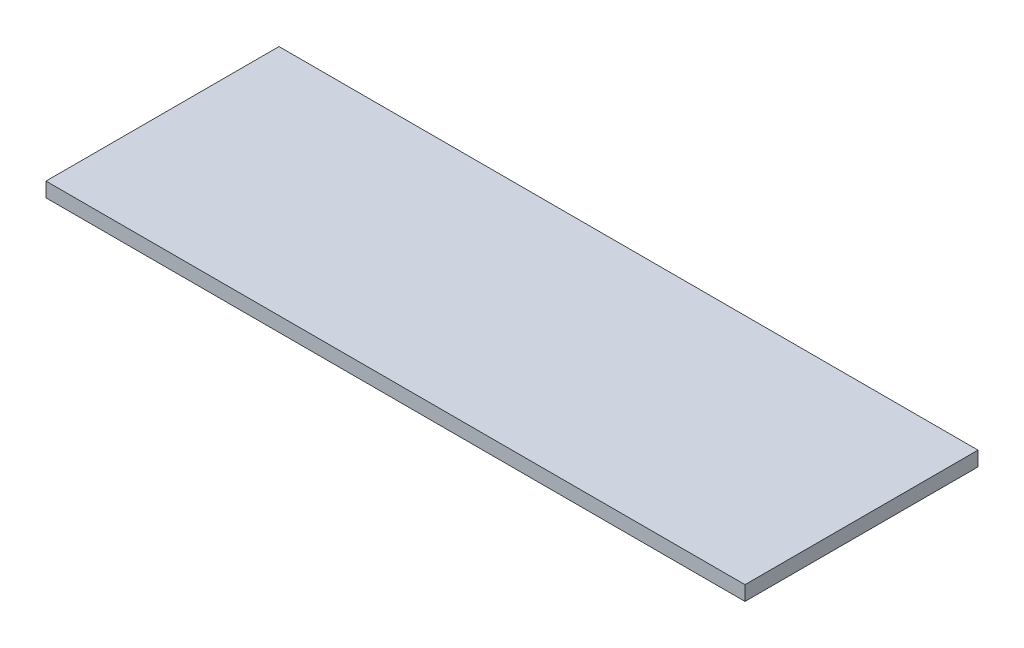
SolidWorks part; units mm, degrees
material "Nylon 101"
ref_plane "Front Plane" through (0, 0, 0) normal (0, 0, 1) x (1, 0, 0)
ref_plane "Top Plane" through (0, 0, 0) normal (0, 1, 0) x (1, 0, 0)
ref_plane "Right Plane" through (0, 0, 0) normal (1, 0, 0) x (0, 0, -1)
sketch "Sketch2" plane through (0, 0, 0) normal (0, 1, 0) x (1, 0, 0)
  line L1 (0, 0) -> (76.2, 0)
  line L2 (0, 0) -> (0, 25.4)
  line L3 (0, 25.4) -> (76.2, 25.4)
  line L4 (76.2, 0) -> (76.2, 25.4)
  dimension "D1" = 25.4
  dimension "D2" = 76.2
extrude "Boss-Extrude1" add sketch "Sketch2" along normal blind 1.5875
